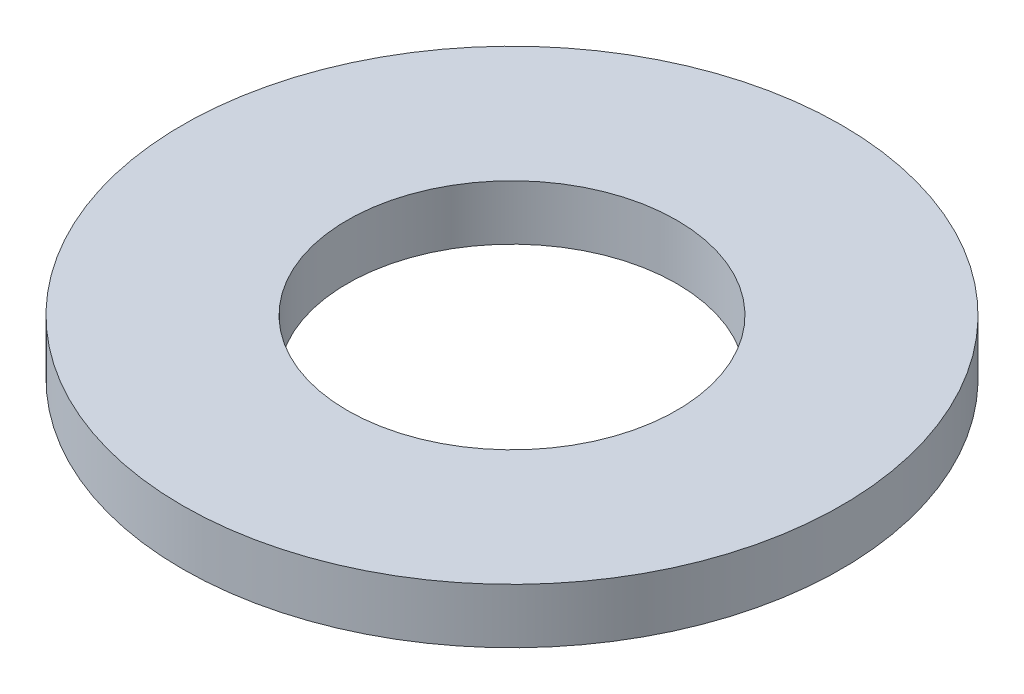
SolidWorks part; units mm, degrees
material "AISI 316 Stainless Steel Sheet (SS)"
ref_plane "Front Plane" through (0, 0, 0) normal (0, 0, 1) x (1, 0, 0)
ref_plane "Top Plane" through (0, 0, 0) normal (0, 1, 0) x (1, 0, 0)
ref_plane "Right Plane" through (0, 0, 0) normal (1, 0, 0) x (0, 0, -1)
sketch "Sketch1" plane through (0, 0, 0) normal (0, 1, 0) x (1, 0, 0)
  circle A0 centre (0, 0) radius 1.5
  circle A1 centre (0, 0) radius 3
  dimension "D1" = 3
  dimension "D2" = 6
extrude "Boss-Extrude1" add sketch "Sketch1" along normal blind 0.5
